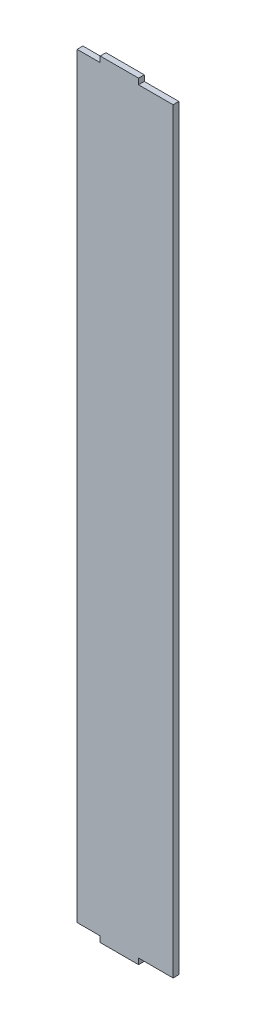
SolidWorks part; units mm, degrees
ref_plane "Alzado" through (0, 0, 0) normal (0, 0, 1) x (1, 0, 0)
ref_plane "Planta" through (0, 0, 0) normal (0, 1, 0) x (1, 0, 0)
ref_plane "Vista lateral" through (0, 0, 0) normal (1, 0, 0) x (0, 0, -1)
sketch "Croquis1" plane through (0, 0, 0) normal (0, 0, 1) x (1, 0, 0)
  line L0 (0, 0) -> (12, 0)
  line L1 (50, 0) -> (50, 394)
  line L2 (50, 394) -> (32, 394)
  line L3 (0, 394) -> (0, 0)
  line L4 (0, 0) -> (12, 0)
  line L5 (12, 0) -> (12, -3)
  line L6 (12, -3) -> (32, -3)
  line L7 (32, -3) -> (32, 0)
  line L8 (0, 394) -> (12, 394)
  line L9 (12, 394) -> (12, 397)
  line L10 (12, 397) -> (32, 397)
  line L11 (32, 397) -> (32, 394)
  line L12 (32, 0) -> (50, 0)
  dimension "D1" = 394
  dimension "D2" = 50
  dimension "D3" = 50
  dimension "D4" = 20
  dimension "D5" = 3
  dimension "D6" = 12
  dimension "D7" = 20
  dimension "D8" = 12
  dimension "D9" = 3
extrude "Saliente-Extruir2" add sketch "Croquis1" along normal blind 3 contours L7 L12 L1 L2 L11 L10 L9 L8 L3 L0 L5 L6
